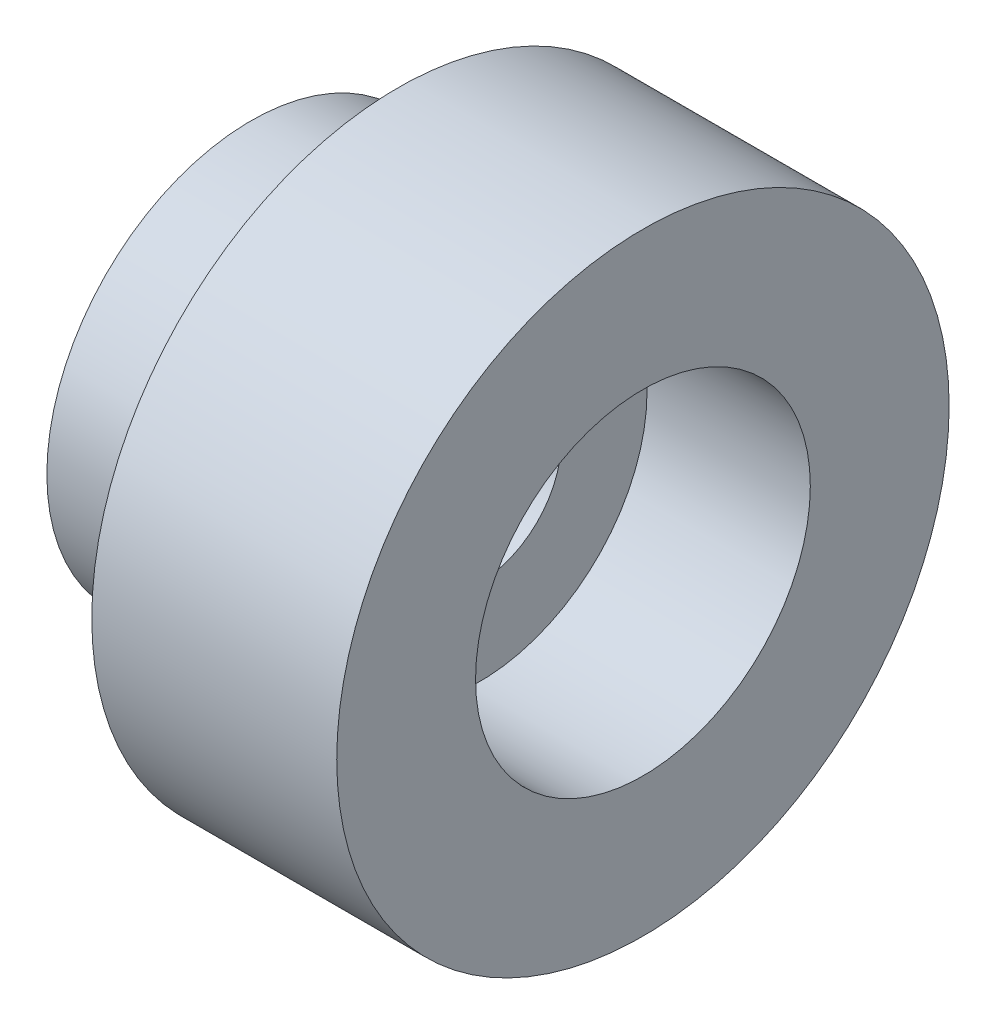
SolidWorks part; units mm, degrees
ref_plane "Front Plane" through (0, 0, 0) normal (0, 0, 1) x (1, 0, 0)
ref_plane "Top Plane" through (0, 0, 0) normal (0, 1, 0) x (1, 0, 0)
ref_plane "Right Plane" through (0, 0, 0) normal (1, 0, 0) x (0, 0, -1)
sketch "Sketch1" plane through (0, 0, 0) normal (0, 0, 1) x (1, 0, 0)
  line L0 (0, 0) -> (7.3225, 0) construction
  line L1 (0, 1) -> (2.8, 1)
  line L2 (2.8, 1) -> (2.8, 2.05)
  line L3 (2.8, 2.05) -> (4.8, 2.05)
  line L4 (4.8, 2.05) -> (4.8, 3.75)
  line L5 (4.8, 3.75) -> (1.8, 3.75)
  line L6 (1.8, 3.75) -> (1.8, 2.5)
  line L7 (1.8, 2.5) -> (0, 2.5)
  line L8 (0, 2.5) -> (0, 1)
  dimension "D1" = 4.1
  dimension "D2" = 2
  dimension "D3" = 5
  dimension "D4" = 7.5
  dimension "D5" = 3
  dimension "D6" = 2
  dimension "D7" = 1.8
revolve "Revolve1" add sketch "Sketch1" angle 360 about L0
